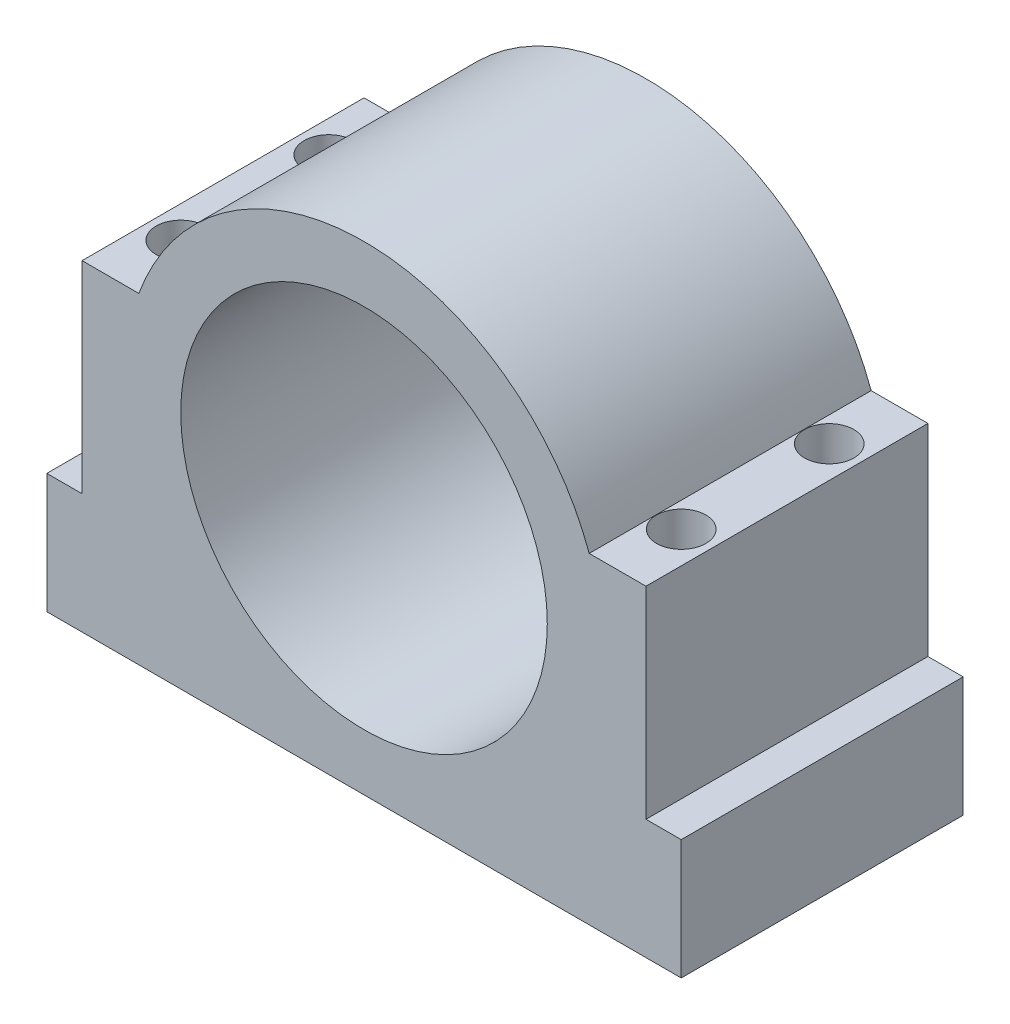
SolidWorks part; units mm, degrees
ref_plane "Front Plane" through (0, 0, 0) normal (0, 0, 1) x (1, 0, 0)
ref_plane "Top Plane" through (0, 0, 0) normal (0, 1, 0) x (1, 0, 0)
ref_plane "Right Plane" through (0, 0, 0) normal (1, 0, 0) x (0, 0, -1)
sketch "Sketch1" plane through (0, 0, 0) normal (0, 0, 1) x (1, 0, 0)
  line L0 (40, 17) -> (45, 17)
  line L1 (-45, 17) -> (-40, 17)
  line L2 (-45, 17) -> (-45, 0)
  line L3 (-45, 0) -> (45, 0)
  line L4 (45, 17) -> (45, 0)
  line L5 (31.9462, 45.6379) -> (40, 45.6379)
  line L6 (-40, 17) -> (-40, 45.6379)
  line L7 (-40, 45.6379) -> (-31.9462, 45.6379)
  line L8 (40, 17) -> (40, 45.6379)
  circle A0 centre (0, 34) radius 26
  arc A1 (31.9462, 45.6379) -> (-31.9462, 45.6379) centre (0, 34) ccw
  point P10 (0, 0)
  point P12 (0, 68)
  point P14 (0, 60)
  dimension "D1" = 52
  dimension "D4" = 34
  dimension "D2" = 90
  dimension "D3" = 34
  dimension "D5" = 90
extrude "Boss-Extrude1" add sketch "Sketch1" along normal blind 40
sketch "Sketch2" plane through (0, 0, 0) normal (0, -1, 0) x (1, 0, 0)
  line L0 (0, 40) -> (0, 0) construction
  line L1 (-45, 40) -> (45, 40) construction
  line L2 (-45, 20) -> (45, 20) construction
  line L3 (-45, 40) -> (-45, 0) construction
  line L4 (45, 40) -> (45, 0) construction
  circle A0 centre (-35.5, 30.5) radius 3.5
  circle A1 centre (-35.5, 9.5) radius 3.5
  circle A2 centre (35.5, 30.5) radius 3.5
  circle A3 centre (35.5, 9.5) radius 3.5
  point P13 (0, 0)
  point P20 (0, 0)
  dimension "D1" = 21
  dimension "D2" = 71
extrude "Cut-Extrude1" cut sketch "Sketch2" against normal blind 100
